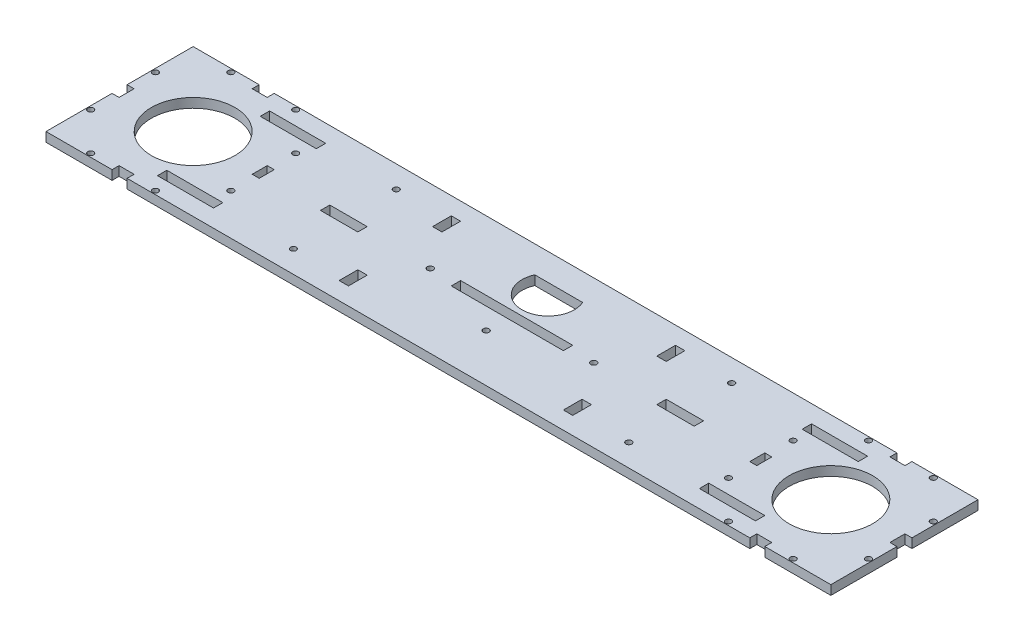
SolidWorks part; units mm, degrees
ref_plane "Front Plane" through (0, 0, 0) normal (0, 0, 1) x (1, 0, 0)
ref_plane "Top Plane" through (0, 0, 0) normal (0, 1, 0) x (1, 0, 0)
ref_plane "Right Plane" through (0, 0, 0) normal (1, 0, 0) x (0, 0, -1)
sketch "Sketch1" plane through (0, 0, 0) normal (0, 1, 0) x (1, 0, 0)
  line L0 (0, 50) -> (0, -51.3531) construction
  line L1 (-266.7, -50) -> (266.7, -50)
  line L2 (-266.7, -50) -> (-266.7, 50)
  line L3 (-266.7, 50) -> (266.7, 50)
  line L4 (266.7, -50) -> (266.7, 50)
  line L7 (-38.1, -3.175) -> (38.1, -3.175)
  line L8 (-38.1, -3.175) -> (-38.1, 3.175)
  line L9 (-38.1, 3.175) -> (38.1, 3.175)
  line L10 (38.1, -3.175) -> (38.1, 3.175)
  line L13 (101.6, 3.175) -> (101.6, -3.175)
  line L14 (-127, 3.175) -> (-101.6, 3.175)
  line L15 (-127, 3.175) -> (-127, -3.175)
  line L16 (-127, -3.175) -> (-101.6, -3.175)
  line L17 (-101.6, 3.175) -> (-101.6, -3.175)
  line L18 (127, -3.175) -> (101.6, -3.175)
  line L19 (127, 3.175) -> (127, -3.175)
  line L20 (127, 3.175) -> (101.6, 3.175)
  line L21 (73.025, -25.4) -> (73.025, -38.1)
  line L22 (-79.375, -25.4) -> (-73.025, -25.4)
  line L23 (-79.375, -25.4) -> (-79.375, -38.1)
  line L24 (-79.375, -38.1) -> (-73.025, -38.1)
  line L25 (-73.025, -25.4) -> (-73.025, -38.1)
  line L26 (79.375, -38.1) -> (73.025, -38.1)
  line L27 (79.375, -25.4) -> (79.375, -38.1)
  line L28 (79.375, -25.4) -> (73.025, -25.4)
  line L30 (79.375, 25.4) -> (73.025, 25.4)
  line L31 (79.375, 25.4) -> (79.375, 38.1)
  line L32 (79.375, 38.1) -> (73.025, 38.1)
  line L33 (73.025, 25.4) -> (73.025, 38.1)
  line L34 (-73.025, 25.4) -> (-73.025, 38.1)
  line L35 (-79.375, 38.1) -> (-73.025, 38.1)
  line L36 (-79.375, 25.4) -> (-79.375, 38.1)
  line L37 (-79.375, 25.4) -> (-73.025, 25.4)
  line L38 (203.5631, -38.1) -> (203.5631, -31.75)
  line L39 (-202.8369, 38.1) -> (-164.7369, 38.1)
  line L40 (-202.8369, 38.1) -> (-202.8369, 31.75)
  line L41 (-202.8369, 31.75) -> (-164.7369, 31.75)
  line L42 (-164.7369, 38.1) -> (-164.7369, 31.75)
  line L43 (165.4631, 38.1) -> (203.5631, 38.1)
  line L44 (165.4631, 38.1) -> (165.4631, 31.75)
  line L45 (165.4631, 31.75) -> (203.5631, 31.75)
  line L46 (203.5631, 38.1) -> (203.5631, 31.75)
  line L47 (165.4631, -31.75) -> (203.5631, -31.75)
  line L48 (165.4631, -38.1) -> (165.4631, -31.75)
  line L49 (165.4631, -38.1) -> (203.5631, -38.1)
  line L50 (-164.7369, -38.1) -> (-164.7369, -31.75)
  line L51 (-202.8369, -31.75) -> (-164.7369, -31.75)
  line L52 (-202.8369, -38.1) -> (-202.8369, -31.75)
  line L53 (-202.8369, -38.1) -> (-164.7369, -38.1)
  line L54 (-16.279, 31.75) -> (16.279, 31.75)
  line L55 (73.025, 31.75) -> (-73.025, 31.75) construction
  line L56 (-115.6157, -34.925) -> (-111.5517, -34.925) construction
  line L57 (-115.6157, -38.1) -> (-115.6157, -31.75) construction
  line L58 (-111.5517, -38.1) -> (-111.5517, -31.75) construction
  line L59 (-113.5837, -31.75) -> (-113.5837, -38.1) construction
  line L60 (-109.6467, -31.75) -> (-117.5207, -31.75) construction
  line L61 (-109.6467, -38.1) -> (-117.5207, -38.1) construction
  line L62 (-59.5451, 0) -> (-51.6123, 0) construction
  line L65 (-55.5625, 3.175) -> (-55.5625, -3.175) construction
  line L66 (-113.5837, 31.75) -> (-113.5837, 38.1) construction
  line L67 (-115.6157, 34.925) -> (-111.5517, 34.925) construction
  line L70 (-51.6255, 3.175) -> (-59.4995, 3.175) construction
  line L71 (-51.6255, -3.175) -> (-59.4995, -3.175) construction
  line L72 (-3.175, -17.5895) -> (3.175, -17.5895) construction
  line L73 (-3.175, -13.6525) -> (-3.175, -21.5265) construction
  line L74 (3.175, -13.6525) -> (3.175, -21.5265) construction
  line L75 (0, -15.5152) -> (0, -21.4943) construction
  arc A0 (-16.279, 31.75) -> (16.279, 31.75) centre (0, 24.6) ccw
  circle A1 centre (-113.5837, -34.925) radius 1.9842
  circle A2 centre (114.3099, 34.925) radius 2.0181
  circle A3 centre (114.3099, -34.925) radius 2.0181
  circle A4 centre (-113.5837, 34.925) radius 1.9842
  circle A5 centre (-55.5625, 0) radius 2.032
  circle A6 centre (55.5625, 0) radius 2.032
  circle A7 centre (0, -17.5895) radius 2.032
  point P0 (0, 0)
  point P6 (0, 0)
  point P96 (-55.5625, 0)
  dimension "D6" = 35.56
  dimension "D7" = 3.9685
  dimension "D8" = 4.064
  dimension "D1" = 100
  dimension "D2" = 533.4
  dimension "D3" = 76.2
  dimension "D4" = 6.35
  dimension "D5" = 25.4
extrude "Boss-Extrude1" add sketch "Sketch1" along normal blind 6.35
sketch "Sketch2" plane through (0, 0, 0) normal (0, 1, 0) x (1, 0, 0)
  line L0 (-238.7, 47.6187) -> (-194.7, 47.6187) construction
  line L1 (-264.3188, 47.6187) -> (-169.0813, 47.6188) construction
  line L2 (-264.3188, 47.6187) -> (-264.3188, -47.6188) construction
  line L3 (-264.3188, -47.6188) -> (-169.0813, -47.6188) construction
  line L4 (-169.0813, 47.6188) -> (-169.0813, -47.6188) construction
  line L5 (-264.3188, 47.6187) -> (-169.0813, -47.6188) construction
  line L6 (-264.3188, -47.6188) -> (-169.0813, 47.6188) construction
  line L7 (-171.4625, -5.1) -> (-166.7, -5.1)
  line L8 (-171.4625, -5.1) -> (-171.4625, 5.1)
  line L9 (-171.4625, 5.1) -> (-166.7, 5.1)
  line L10 (-166.7, -5.1) -> (-166.7, 5.1)
  line L11 (-171.4625, -5.1) -> (-166.7, 5.1) construction
  line L12 (-171.4625, 5.1) -> (-166.7, -5.1) construction
  line L13 (-266.7, -5.1) -> (-261.9375, -5.1)
  line L14 (-266.7, -5.1) -> (-266.7, 5.1)
  line L15 (-266.7, 5.1) -> (-261.9375, 5.1)
  line L16 (-261.9375, -5.1) -> (-261.9375, 5.1)
  line L17 (-266.7, -5.1) -> (-261.9375, 5.1) construction
  line L18 (-266.7, 5.1) -> (-261.9375, -5.1) construction
  line L19 (-221.8, 50) -> (-211.6, 50)
  line L20 (-221.8, 50) -> (-221.8, 45.2375)
  line L21 (-221.8, 45.2375) -> (-211.6, 45.2375)
  line L22 (-211.6, 50) -> (-211.6, 45.2375)
  line L23 (-221.8, 50) -> (-211.6, 45.2375) construction
  line L24 (-221.8, 45.2375) -> (-211.6, 50) construction
  line L25 (-221.8, -45.2375) -> (-211.6, -45.2375)
  line L26 (-221.8, -45.2375) -> (-221.8, -50)
  line L27 (-221.8, -50) -> (-211.6, -50)
  line L28 (-211.6, -45.2375) -> (-211.6, -50)
  line L29 (-221.8, -45.2375) -> (-211.6, -50) construction
  line L30 (-221.8, -50) -> (-211.6, -45.2375) construction
  line L31 (-169.0813, 22) -> (-169.0813, -22) construction
  line L32 (-194.7, -47.6188) -> (-238.7, -47.6188) construction
  line L33 (-264.3188, -22) -> (-264.3188, 22) construction
  line L34 (-266.7, -50) -> (-266.7, 50) construction
  line L35 (0, 50) -> (0, -7.3454) construction
  line L37 (264.3188, -22) -> (264.3187, 22) construction
  line L38 (194.7, -47.6187) -> (238.7, -47.6187) construction
  line L39 (169.0812, 22) -> (169.0813, -22) construction
  line L40 (221.8, -50) -> (211.6, -45.2375) construction
  line L41 (221.8, -45.2375) -> (211.6, -50) construction
  line L42 (221.8, 45.2375) -> (211.6, 50) construction
  line L43 (221.8, 50) -> (211.6, 45.2375) construction
  line L44 (266.7, 5.1) -> (261.9375, -5.1) construction
  line L45 (266.7, -5.1) -> (261.9375, 5.1) construction
  line L46 (171.4625, 5.1) -> (166.7, -5.1) construction
  line L47 (-266.7, 50) -> (266.7, 50) construction
  line L48 (171.4625, -5.1) -> (166.7, 5.1) construction
  line L49 (264.3188, -47.6187) -> (169.0812, 47.6188) construction
  line L50 (264.3187, 47.6188) -> (169.0813, -47.6187) construction
  line L51 (169.0812, 47.6188) -> (169.0813, -47.6187) construction
  line L52 (264.3188, -47.6187) -> (169.0813, -47.6187) construction
  line L53 (264.3187, 47.6188) -> (264.3188, -47.6187) construction
  line L54 (264.3187, 47.6188) -> (169.0812, 47.6188) construction
  line L55 (238.7, 47.6188) -> (194.7, 47.6188) construction
  line L56 (211.6, -45.2375) -> (211.6, -50)
  line L57 (221.8, -50) -> (211.6, -50)
  line L58 (221.8, -45.2375) -> (221.8, -50)
  line L59 (221.8, -45.2375) -> (211.6, -45.2375)
  line L60 (211.6, 50) -> (211.6, 45.2375)
  line L61 (221.8, 45.2375) -> (211.6, 45.2375)
  line L62 (221.8, 50) -> (221.8, 45.2375)
  line L63 (221.8, 50) -> (211.6, 50)
  line L64 (261.9375, -5.1) -> (261.9375, 5.1)
  line L65 (266.7, 5.1) -> (261.9375, 5.1)
  line L66 (266.7, -5.1) -> (266.7, 5.1)
  line L67 (266.7, -5.1) -> (261.9375, -5.1)
  line L68 (166.7, -5.1) -> (166.7, 5.1)
  line L69 (171.4625, 5.1) -> (166.7, 5.1)
  line L70 (171.4625, -5.1) -> (171.4625, 5.1)
  line L71 (171.4625, -5.1) -> (166.7, -5.1)
  circle A0 centre (-169.0813, 22) radius 1.9844
  circle A1 centre (-169.0813, -22) radius 1.9844
  circle A2 centre (-194.7, -47.6188) radius 1.9844
  circle A3 centre (-238.7, -47.6188) radius 1.9844
  circle A4 centre (-264.3188, -22) radius 1.9844
  circle A5 centre (-264.3188, 22) radius 1.9844
  circle A6 centre (-194.7, 47.6187) radius 1.9844
  circle A7 centre (-238.7, 47.6187) radius 1.9844
  circle A8 centre (-216.7, 0) radius 28.36
  circle A9 centre (216.7, 0) radius 28.36
  circle A10 centre (238.7, 47.6188) radius 1.9844
  circle A11 centre (194.7, 47.6188) radius 1.9844
  circle A12 centre (264.3187, 22) radius 1.9844
  circle A13 centre (264.3188, -22) radius 1.9844
  circle A14 centre (238.7, -47.6187) radius 1.9844
  circle A15 centre (194.7, -47.6187) radius 1.9844
  circle A16 centre (169.0813, -22) radius 1.9844
  circle A17 centre (169.0812, 22) radius 1.9844
  point P0 (-216.7, 0)
  point P5 (-169.0813, 0)
  point P11 (-264.3188, 0)
  point P16 (-216.7, 47.6187)
  point P21 (-216.7, -47.6187)
  point P42 (-216.7, 17.6187)
  point P89 (216.7, 17.6188)
  point P90 (216.7, -47.6187)
  point P91 (216.7, 47.6188)
  point P92 (264.3187, 0)
  point P93 (169.0813, 0)
  dimension "D6" = 3.9688
  dimension "D2" = 2.3813
  dimension "D3" = 10.2
  dimension "D4" = 4.7625
  dimension "D5" = 44
  dimension "D12" = 2.3813
extrude "Cut-Extrude2" cut sketch "Sketch2" along normal blind 6.35
